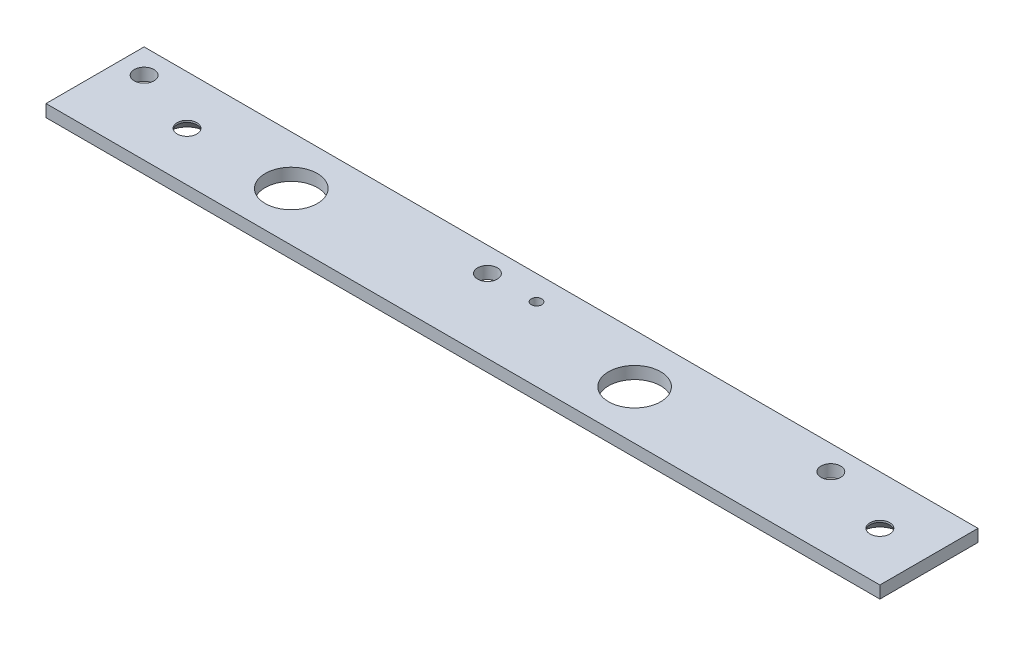
SolidWorks part; units mm, degrees
material "Copper"
ref_plane "Front Plane" through (0, 0, 0) normal (0, 0, 1) x (1, 0, 0)
ref_plane "Top Plane" through (0, 0, 0) normal (0, 1, 0) x (1, 0, 0)
ref_plane "Right Plane" through (0, 0, 0) normal (1, 0, 0) x (0, 0, -1)
sketch "Sketch1" plane through (0, 0, 0) normal (1, 0, 0) x (0, 0, -1)
  line L1 (-12.7, 1.5875) -> (12.7, 1.5875)
  line L2 (-12.7, 1.5875) -> (-12.7, -1.5875)
  line L3 (-12.7, -1.5875) -> (12.7, -1.5875)
  line L4 (12.7, 1.5875) -> (12.7, -1.5875)
  line L5 (-12.7, 1.5875) -> (12.7, -1.5875) construction
  line L6 (-12.7, -1.5875) -> (12.7, 1.5875) construction
  point P0 (0, 0)
  dimension "D1" = 25.4
  dimension "D2" = 3.175
extrude "Boss-Extrude1" add sketch "Sketch1" along normal mid plane 215.9
hole_wizard "#10 Clearance Hole1" positions "Sketch2" profile "Sketch3" hole size "#10" standard "ANSI Inch" end condition through all
sketch "Sketch2" plane through (0, 1.5875, 0) normal (0, 1, 0) x (1, 0, 0)
  line L1 (-107.95, 12.7) -> (-107.95, -12.7) construction
  line L2 (107.95, 12.7) -> (-107.95, 12.7) construction
  point P0 (-101.6, 6.35)
  point P2 (-12.7, 6.35)
  point P4 (76.2, 6.35)
  dimension "D1" = 6.35
  dimension "D2" = 6.35
  dimension "D3" = 88.9
  dimension "D4" = 88.9
sketch "Sketch3" plane through (-101.6, 1.5875, -6.35) normal (1, 0, 0) x (0, 0, 1)
  line L0 (0, 0) -> (0, 3.175)
  line L1 (0, 3.175) -> (2.5527, 3.175)
  line L2 (2.5527, 3.175) -> (2.5527, 0)
  line L5 (2.5527, 0) -> (0, 0)
  line L11 (0, -6.35) -> (0, 107.95) construction
  dimension "Thru Hole Dia." = 5.1054
  dimension "Thru Hole Depth" = 3.175
hole_wizard "1/2 Clearance Hole1" positions "Sketch4" profile "Sketch5" hole size "1/2" standard "ANSI Inch" end condition through all
sketch "Sketch4" plane through (0, 1.5875, 0) normal (0, 1, 0) x (1, 0, 0)
  line L0 (-101.6, 6.35) -> (-57.15, 0) construction
  line L1 (-57.15, 0) -> (-12.7, 6.35) construction
  line L2 (-12.7, 6.35) -> (31.75, 0) construction
  line L3 (31.75, 0) -> (76.2, 6.35) construction
  line L5 (107.95, -12.7) -> (-107.95, -12.7) construction
  point P0 (-57.15, 0)
  point P2 (31.75, 0)
  dimension "D1" = 12.7
sketch "Sketch5" plane through (-57.15, 1.5875, 0) normal (1, 0, 0) x (0, 0, 1)
  line L0 (0, 0) -> (0, 3.175)
  line L1 (0, 3.175) -> (6.7462, 3.175)
  line L2 (6.7462, 3.175) -> (6.7462, 0)
  line L5 (6.7462, 0) -> (0, 0)
  line L11 (0, -6.35) -> (0, 107.95) construction
  dimension "Thru Hole Dia." = 13.4925
  dimension "Thru Hole Depth" = 3.175
hole_wizard "#6-32 Tapped Hole1" positions "Sketch6" profile "Sketch7" tap size "#6-32" standard "ANSI Inch" end condition through all
sketch "Sketch6" plane through (0, 1.5875, 0) normal (0, 1, 0) x (1, 0, 0)
  line L0 (107.95, 12.7) -> (-107.95, 12.7) construction
  circle A0 centre (-12.7, 6.35) radius 2.5527 construction
  point P0 (0, 6.35)
  dimension "D1" = 12.7
  dimension "D2" = 6.35
sketch "Sketch7" plane through (0, 1.5875, -6.35) normal (1, 0, 0) x (0, 0, 1)
  line L0 (0, 0) -> (0, 3.175)
  line L1 (0, 3.175) -> (1.3525, 3.175)
  line L2 (1.3525, 3.175) -> (1.3525, 0)
  line L5 (1.3525, 0) -> (0, 0)
  line L11 (0, -6.35) -> (0, 107.95) construction
  dimension "Thru Tap Drill Dia." = 2.7051
  dimension "Thru Tap Drill Depth" = 3.175
cosmetic thread "Hole Thread1"
hole_wizard "CSK for #10 Flat Head Machine Screw1" positions "Sketch8" profile "Sketch9" countersink size "#10" standard "ANSI Inch" end condition through all
sketch "Sketch8" plane through (171.45, -1.5875, -50.8) normal (0, -1, 0) x (-1, 0, 0)
  point P0 (76.2, -101.6)
  point P3 (76.2, -50.8)
  point P6 (255.5875, -50.8)
  point P9 (255.5875, -101.6)
  point P12 (-255.5875, -101.6)
  point P15 (-76.2, -101.6)
  point P18 (-76.2, -50.8)
  point P21 (-255.5875, -50.8)
sketch "Sketch9" plane through (95.25, -1.5875, 50.8) normal (1, 0, 0) x (0, 0, -1)
  line L0 (0, 0) -> (0, 3.175)
  line L1 (0, 3.175) -> (2.5527, 3.175)
  line L2 (2.5527, 3.175) -> (2.5527, 2.6882)
  line L3 (2.5527, 2.6882) -> (4.8895, 0)
  line L4 (4.8895, 0) -> (0, 0)
  line L5 (-2.5527, 2.6882) -> (-4.8895, 0) construction
  line L6 (0, -6.35) -> (0, 107.95) construction
  dimension "Thru Hole Dia." = 5.1054
  dimension "Thru Hole Depth" = 3.175
  dimension "Near C'Sink Dia." = 9.779
  dimension "Near C'Sink Angle" = 82
